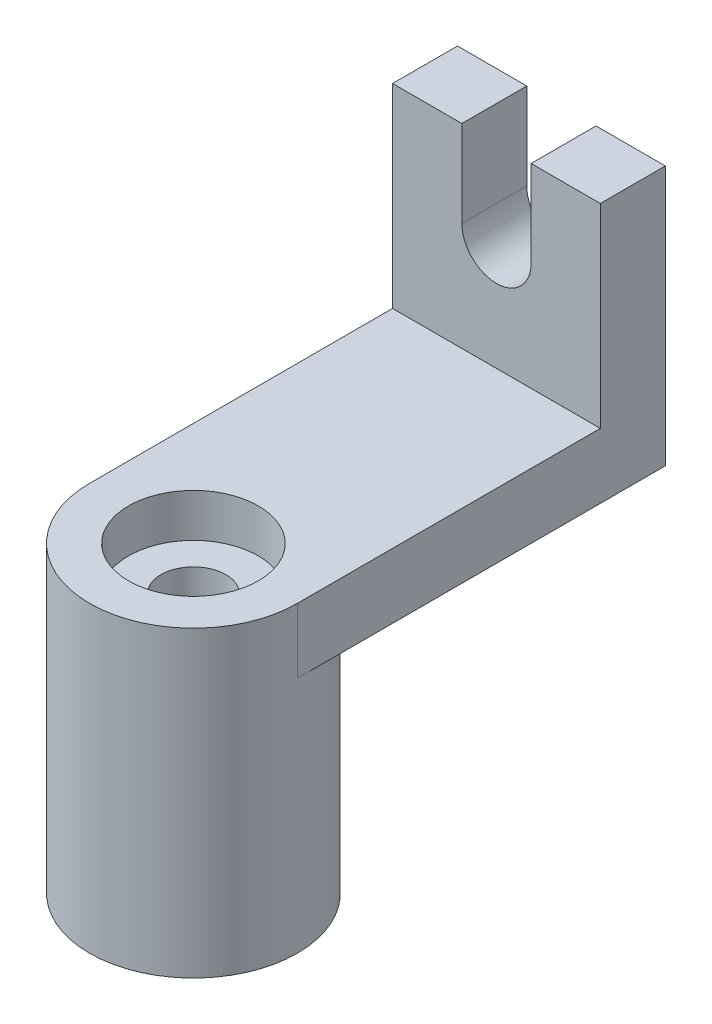
SolidWorks part; units mm, degrees
ref_plane "Front Plane" through (0, 0, 0) normal (0, 0, 1) x (1, 0, 0)
ref_plane "Top Plane" through (0, 0, 0) normal (0, 1, 0) x (1, 0, 0)
ref_plane "Right Plane" through (0, 0, 0) normal (1, 0, 0) x (0, 0, -1)
sketch "Sketch1" plane through (0, 0, 0) normal (0, 1, 0) x (1, 0, 0)
  circle A0 centre (0, 0) radius 24
  circle A1 centre (0, 0) radius 7.5
  dimension "D1" = 15
  dimension "D2" = 48
extrude "Boss-Extrude1" add sketch "Sketch1" along normal blind 70
sketch "Sketch2" plane through (0, 0, 0) normal (1, 0, 0) x (0, 0, -1)
  line L0 (0, 55) -> (85, 55)
  line L1 (85, 55) -> (85, 115)
  line L2 (85, 115) -> (70, 115)
  line L3 (70, 115) -> (70, 70)
  line L4 (70, 70) -> (0, 70)
  line L5 (0, 70) -> (0, 55)
  line L6 (-24, 0) -> (24, 0) construction
  dimension "D1" = 55
  dimension "D2" = 15
  dimension "D3" = 15
  dimension "D4" = 85
  dimension "D5" = 70
  dimension "D6" = 60
extrude "Boss-Extrude3" add sketch "Sketch2" along normal mid plane 48
sketch "Sketch3" plane through (0, 55, 0) normal (0, -1, 0) x (-1, 0, 0)
  circle A0 centre (0, 0) radius 7.5
extrude "Cut-Extrude1" cut sketch "Sketch3" against normal blind 48
sketch "Sketch4" plane through (0, 70, 0) normal (0, 1, 0) x (1, 0, 0)
  circle A0 centre (0, 0) radius 15
  dimension "D1" = 30
extrude "Cut-Extrude2" cut sketch "Sketch4" against normal blind 10
sketch "Sketch5" plane through (0, 0, 0) normal (0, -1, 0) x (1, 0, 0)
  circle A0 centre (0, 0) radius 15
  dimension "D1" = 30
extrude "Cut-Extrude3" cut sketch "Sketch5" against normal blind 10
sketch "Sketch6" plane through (0, 0, -85) normal (0, 0, -1) x (-1, 0, 0)
  line L0 (-24, 115) -> (24, 115) construction
  line L1 (-8, 95) -> (-8, 115)
  line L2 (8, 95) -> (8, 115)
  line L3 (-8, 115) -> (8, 115)
  arc A0 (-8, 95) -> (8, 95) centre (0, 95) ccw
  dimension "D1" = 16
  dimension "D2" = 20
extrude "Cut-Extrude4" cut sketch "Sketch6" against normal blind 20
